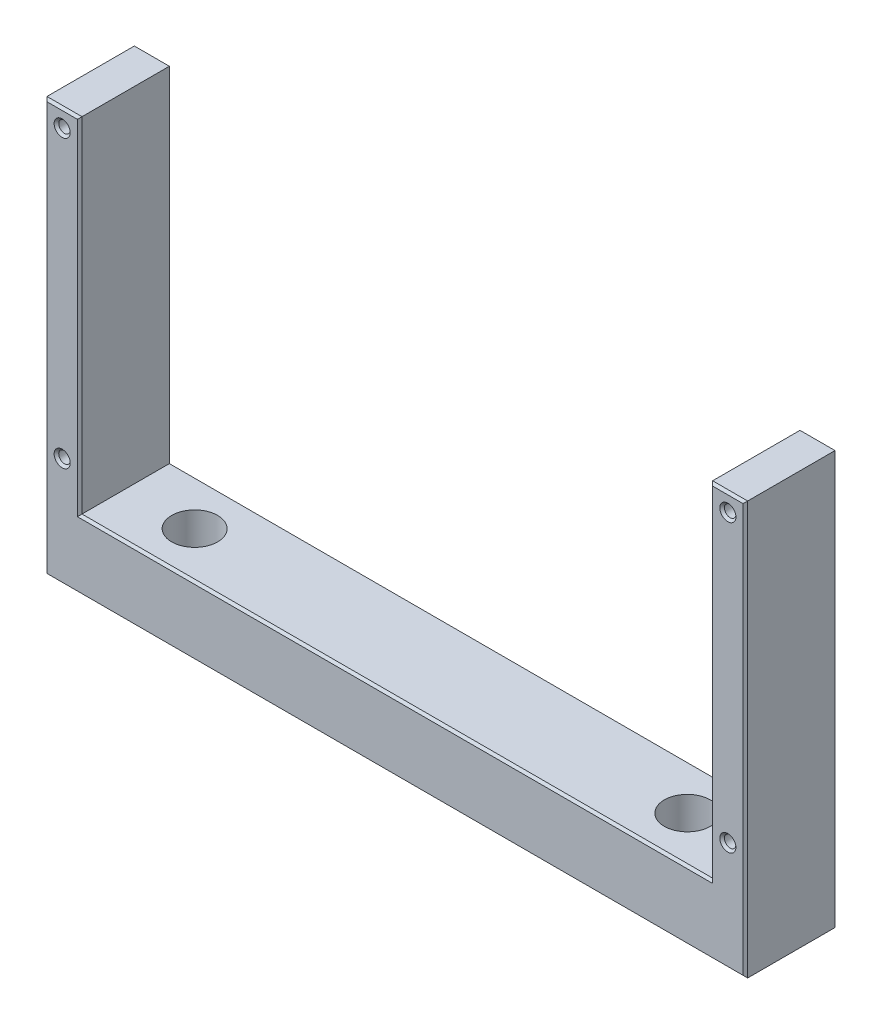
SolidWorks part; units mm, degrees
ref_plane "Front Plane" through (0, 0, 0) normal (0, 0, 1) x (1, 0, 0)
ref_plane "Top Plane" through (0, 0, 0) normal (0, 1, 0) x (1, 0, 0)
ref_plane "Right Plane" through (0, 0, 0) normal (1, 0, 0) x (0, 0, -1)
sketch "Sketch1" plane through (0, 0, 0) normal (0, 0, 1) x (1, 0, 0)
  line L1 (-72.39, 31.115) -> (72.39, 31.115)
  line L2 (-72.39, 31.115) -> (-72.39, -31.115)
  line L3 (-72.39, -31.115) -> (72.39, -31.115)
  line L4 (72.39, 31.115) -> (72.39, -31.115)
  line L5 (-72.39, 31.115) -> (72.39, -31.115) construction
  line L6 (-72.39, -31.115) -> (72.39, 31.115) construction
  line L7 (76.2, 34.925) -> (-76.2, 34.925)
  line L8 (76.2, 34.925) -> (76.2, -34.925)
  line L9 (76.2, -34.925) -> (-76.2, -34.925)
  line L10 (-76.2, 34.925) -> (-76.2, -34.925)
  line L11 (76.2, 34.925) -> (-76.2, -34.925) construction
  line L12 (76.2, -34.925) -> (-76.2, 34.925) construction
  point P0 (0, 0)
  point P6 (0, 0)
  dimension "D1" = 144.78
  dimension "D2" = 62.23
  dimension "D3" = 152.4
  dimension "D4" = 69.85
sketch "Sketch2" plane through (0, 0, 0) normal (0, 0, 1) x (1, 0, 0)
  line L0 (-76.2, 34.925) -> (-68.58, 34.925)
  line L1 (76.2, 34.925) -> (-76.2, 34.925) construction
  line L2 (-68.58, 34.925) -> (-68.58, -39.925)
  line L4 (-68.58, -39.925) -> (68.58, -39.925)
  line L5 (68.58, -39.925) -> (68.58, 34.925)
  line L6 (68.58, 34.925) -> (76.2, 34.925)
  line L7 (76.2, 34.925) -> (76.2, -54.925)
  line L8 (76.2, -54.925) -> (-76.2, -54.925)
  line L9 (-76.2, -54.925) -> (-76.2, 34.925)
  line L10 (-72.39, 31.115) -> (-72.39, 34.925) construction
  line L11 (76.2, -34.925) -> (-76.2, -34.925) construction
  dimension "D1" = 15
  dimension "D2" = 5
extrude "Boss-Extrude1" add sketch "Sketch2" along normal blind 20
hole_wizard "M3x0.5 Tapped Hole1" positions "Sketch3" profile "Sketch4" tap size "M3x0.5" standard "ANSI Metric" end condition through all
sketch "Sketch3" plane through (0, 0, 0) normal (0, 0, -1) x (-1, 0, 0)
  point P0 (-72.39, -31.115)
  point P3 (-72.39, 31.115)
  point P6 (72.39, 31.115)
  point P9 (72.39, -31.115)
sketch "Sketch4" plane through (72.39, -31.115, 0) normal (1, 0, 0) x (0, 1, 0)
  line L0 (0, 0) -> (0, 20)
  line L1 (0, 20) -> (1.25, 20)
  line L2 (1.25, 20) -> (1.25, 0)
  line L5 (1.25, 0) -> (0, 0)
  line L11 (0, -6.35) -> (0, 107.95) construction
  dimension "Thru Tap Drill Dia." = 2.5
  dimension "Thru Tap Drill Depth" = 20
cosmetic thread "Hole Thread1" parameters "D2"=3
cosmetic thread "Hole Thread2" parameters "D2"=3
cosmetic thread "Hole Thread3" parameters "D2"=3
cosmetic thread "Hole Thread4" parameters "D2"=3
chamfer "Chamfer1" distance 0.5 angle 45 24 edges at (0, -54.925, 0) (76.2, -10, 0) (72.39, 34.925, 0) (68.58, -2.5, 0) (0, -39.925, 0) (-68.58, -2.5, 0) (-72.39, 34.925, 0) (-76.2, -10, 0) (-73.64, -31.115, 0) (-73.64, 31.115, 0) (71.14, 31.115, 0) (71.14, -31.115, 0) (-72.39, 34.925, 20) (-68.58, -2.5, 20) (0, -39.925, 20) (68.58, -2.5, 20) (72.39, 34.925, 20) (76.2, -10, 20) (0, -54.925, 20) (-76.2, -10, 20) (-73.64, -31.115, 20) (-73.64, 31.115, 20) (71.14, 31.115, 20) (71.14, -31.115, 20)
hole_wizard "CBORE for M5 SHCS1" positions "3DSketch1" profile "Sketch6" counterbore size "M5" standard "ANSI Metric" end condition through all
sketch3d "3DSketch1"
  line L0 (-68.58, -39.925, 10) -> (68.58, -39.925, 10)
  line L1 (-68.58, -39.925, 19.5) -> (-68.58, -39.925, 0.5) construction
  line L2 (68.58, -39.925, 19.5) -> (68.58, -39.925, 0.5) construction
  point P1 (-53.58, -39.925, 10)
  point P3 (53.58, -39.925, 10)
  dimension "D1" = 15
  dimension "D2" = 15
sketch "Sketch6" plane through (-53.58, -39.925, 10) normal (1, 0, 0) x (0, 0, 1)
  line L0 (0, 0) -> (0, 15)
  line L1 (0, 15) -> (2.75, 15)
  line L3 (2.75, 15) -> (2.75, 10)
  line L4 (2.75, 10) -> (5, 10)
  line L5 (5, 10) -> (5, 0)
  line L7 (5, 0) -> (0, 0)
  line L11 (0, -6.35) -> (0, 107.95) construction
  dimension "Thru Hole Dia." = 5.5
  dimension "Thru Hole Depth" = 15
  dimension "C'Bore Dia." = 10
  dimension "C'Bore Depth" = 10
